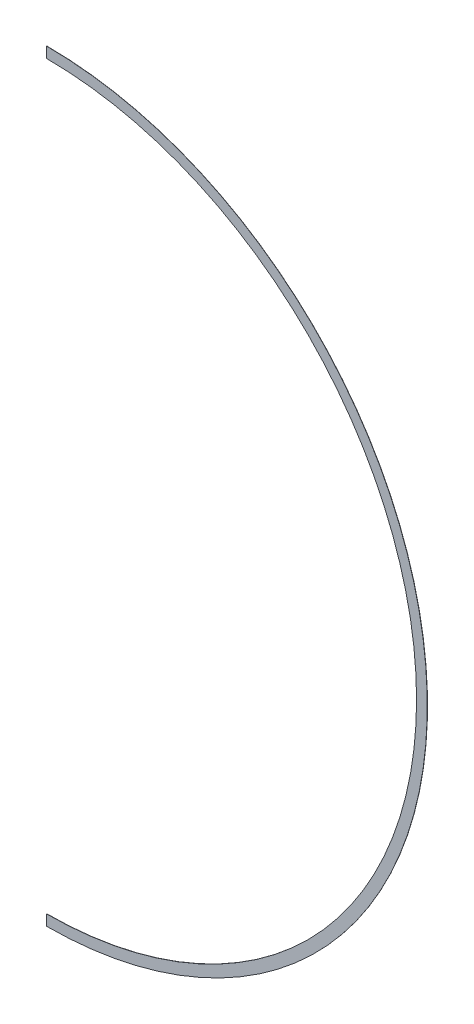
SolidWorks part; units mm, degrees
material "PET"
ref_plane "Front Plane" through (0, 0, 0) normal (0, 0, 1) x (1, 0, 0)
ref_plane "Top Plane" through (0, 0, 0) normal (0, 1, 0) x (1, 0, 0)
ref_plane "Right Plane" through (0, 0, 0) normal (1, 0, 0) x (0, 0, -1)
sketch "Sketch1" plane through (0, 0, 0) normal (0, 0, 1) x (1, 0, 0)
  line L0 (0, 213) -> (0, 207)
  line L1 (0, -207) -> (0, -213)
  arc A0 (0, 207) -> (0, -207) centre (0, 0) cw
  arc A1 (0, 213) -> (0, -213) centre (0, 0) cw
  dimension "D1" = 426
  dimension "D2" = 414
extrude "Boss-Extrude1" add sketch "Sketch1" along normal blind 0.127
sketch "Sketch2" plane through (0, 0, 0.127) normal (0, 0, 1) x (1, 0, 0)
  line L0 (0, 213) -> (0, -213)
  line L1 (0, 213) -> (0.25, 213)
  line L2 (0, -213) -> (0.25, -213)
  line L3 (0.25, 213) -> (0.25, -213)
  dimension "D1" = 0.25
extrude "Cut-Extrude1" cut sketch "Sketch2" against normal through all
